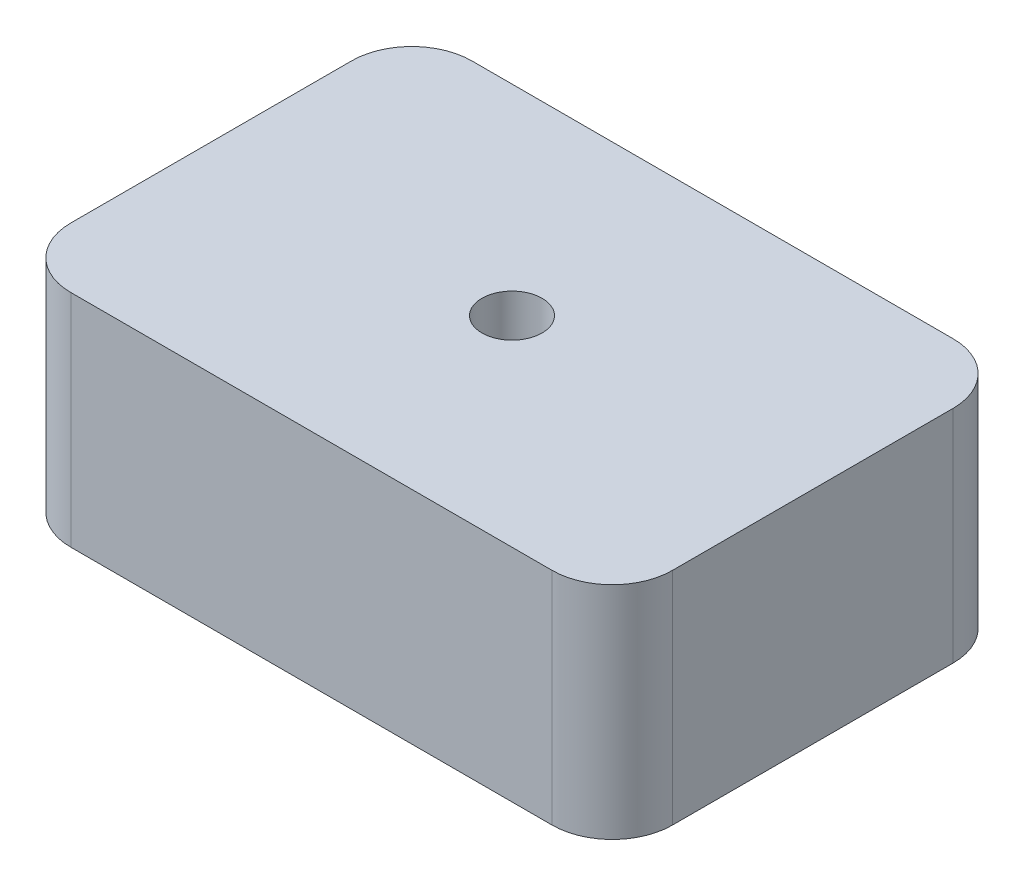
SolidWorks part; units mm, degrees
material "ABS"
ref_plane "Front Plane" through (0, 0, 0) normal (0, 0, 1) x (1, 0, 0)
ref_plane "Top Plane" through (0, 0, 0) normal (0, 1, 0) x (1, 0, 0)
ref_plane "Right Plane" through (0, 0, 0) normal (1, 0, 0) x (0, 0, -1)
sketch "Sketch1" plane through (0, 0, 0) normal (0, 1, 0) x (1, 0, 0)
  line L1 (-75, -50) -> (75, -50)
  line L2 (-75, -50) -> (-75, 50)
  line L3 (-75, 50) -> (75, 50)
  line L4 (75, -50) -> (75, 50)
  line L5 (-75, -50) -> (75, 50) construction
  line L6 (-75, 50) -> (75, -50) construction
  circle A0 centre (0, 0) radius 7.5
  point P0 (0, 0)
  dimension "D1" = 15
  dimension "D2" = 150
  dimension "D3" = 100
extrude "Boss-Extrude1" add sketch "Sketch1" along normal blind 55
fillet "Fillet1" radius 15 4 edges at (75, 27.5, -50) (-75, 27.5, -50) (-75, 27.5, 50) (75, 27.5, 50)
